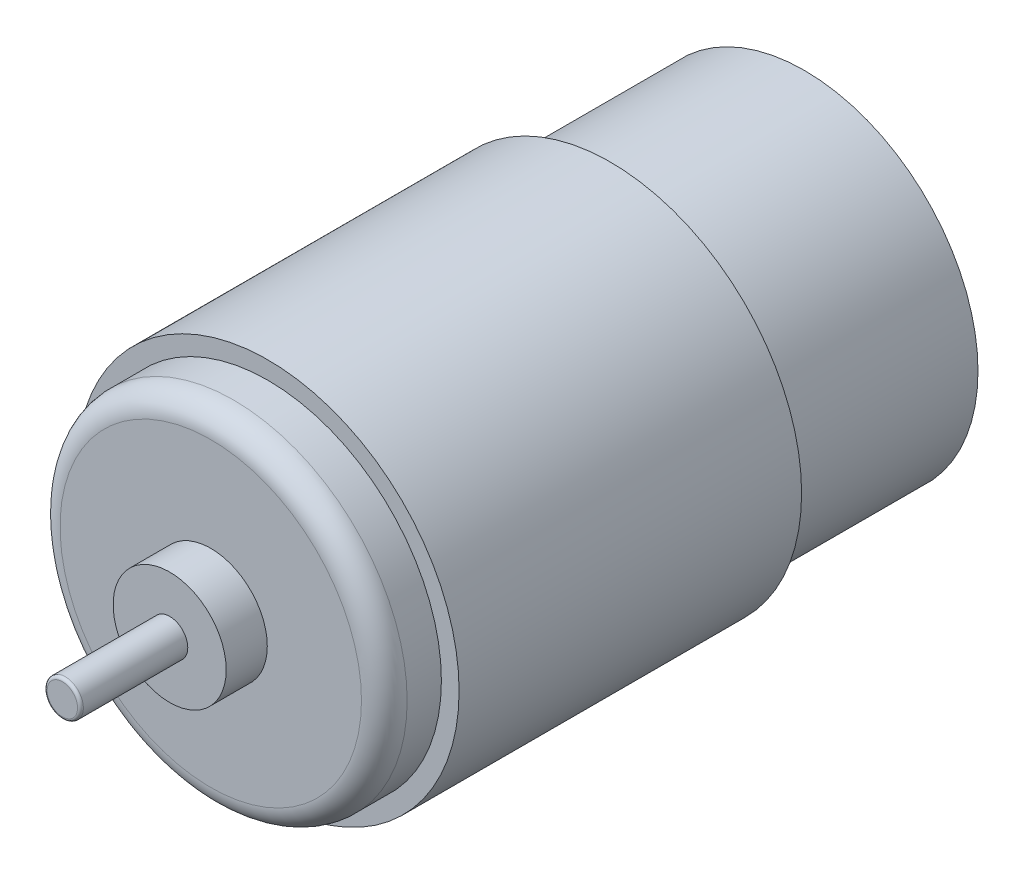
SolidWorks part; units mm, degrees
ref_plane "Front Plane" through (0, 0, 0) normal (0, 0, 1) x (1, 0, 0)
ref_plane "Top Plane" through (0, 0, 0) normal (0, 1, 0) x (1, 0, 0)
ref_plane "Right Plane" through (0, 0, 0) normal (1, 0, 0) x (0, 0, -1)
sketch "Sketch1" plane through (0, 0, 0) normal (0, 0, 1) x (1, 0, 0)
  circle A0 centre (0, 0) radius 16.75
  dimension "D1" = 33.5
extrude "Boss-Extrude1" add sketch "Sketch1" along normal blind 30
sketch "Sketch2" plane through (0, 0, 30) normal (0, 0, 1) x (1, 0, 0)
  circle A0 centre (0, 0) radius 15.2
  dimension "D1" = 30.4
extrude "Boss-Extrude2" add sketch "Sketch2" along normal blind 5
fillet "Fillet1" radius 2 1 edges at (15.2, 0, 35)
sketch "Sketch3" plane through (0, 0, 0) normal (0, 0, -1) x (-1, 0, 0)
  circle A0 centre (0, 0) radius 15.2
  dimension "D1" = 30.4
extrude "Boss-Extrude3" add sketch "Sketch3" along normal blind 17
sketch "Sketch4" plane through (0, 0, 35) normal (0, 0, 1) x (1, 0, 0)
  circle A0 centre (0, 0) radius 4.95
  dimension "D1" = 9.9
extrude "Boss-Extrude4" add sketch "Sketch4" along normal blind 3.6
sketch "Sketch5" plane through (0, 0, -17) normal (0, 0, -1) x (-1, 0, 0)
  circle A0 centre (0, 0) radius 5
  dimension "D1" = 10
extrude "Boss-Extrude5" add sketch "Sketch5" along normal blind 2.6
sketch "Sketch6" plane through (0, 0, 38.6) normal (0, 0, 1) x (1, 0, 0)
  circle A0 centre (0, 0) radius 1.585
  dimension "D1" = 3.17
extrude "Boss-Extrude6" add sketch "Sketch6" along normal blind 9.4
fillet "Fillet2" radius 0.254 1 edges at (1.585, 0, 48)
